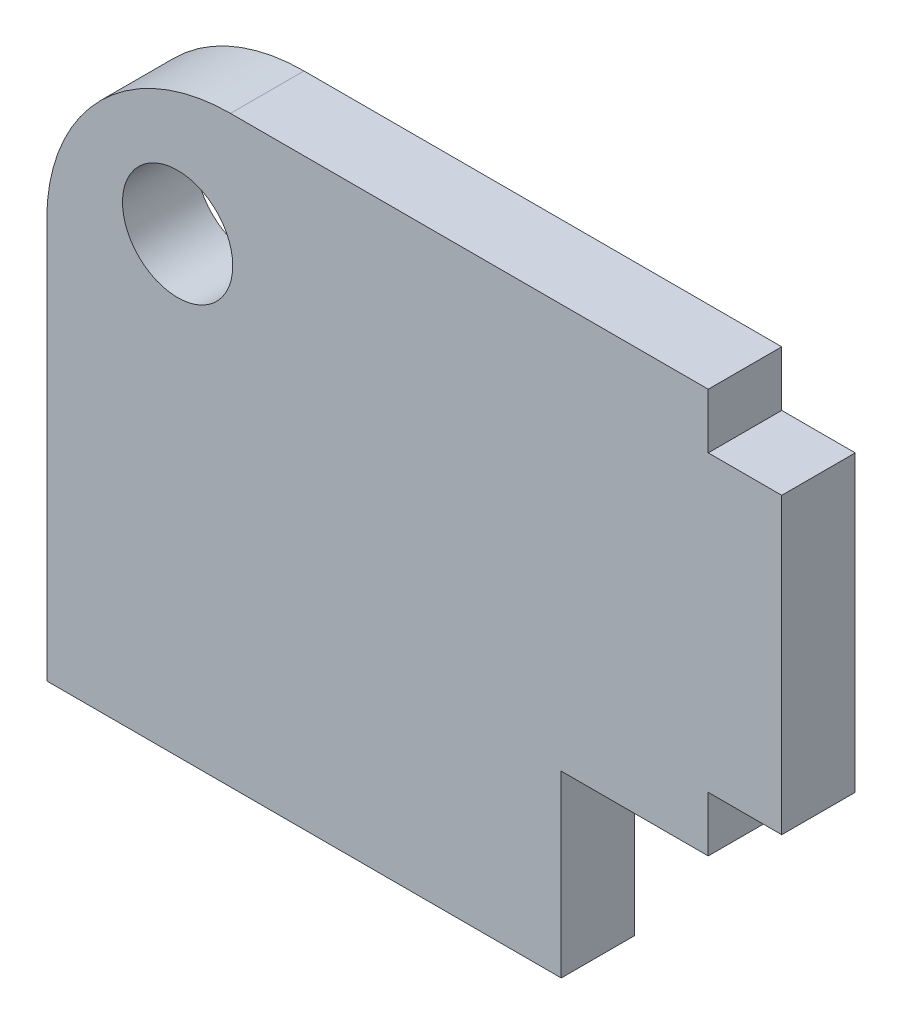
SolidWorks part; units mm, degrees
ref_plane "Front Plane" through (0, 0, 0) normal (0, 0, 1) x (1, 0, 0)
ref_plane "Top Plane" through (0, 0, 0) normal (0, 1, 0) x (1, 0, 0)
ref_plane "Right Plane" through (0, 0, 0) normal (1, 0, 0) x (0, 0, -1)
sketch "Sketch1" plane through (0, 0, 0) normal (0, 0, 1) x (1, 0, 0)
  line L0 (10, -1.5622) -> (8, -1.5622)
  line L1 (4, -7.9378) -> (-10, -7.9378)
  line L2 (4, -7.9378) -> (4, -3.0622)
  line L3 (10, 6.4378) -> (10, -1.5622)
  line L4 (-5, 7.9378) -> (8, 7.9378)
  line L5 (8, 6.4378) -> (8, 7.9378)
  line L6 (10, 6.4378) -> (8, 6.4378)
  line L7 (-10, -7.9378) -> (-10, 2.9378)
  line L8 (8, -1.5622) -> (8, -3.0622)
  line L9 (8, -3.0622) -> (4, -3.0622)
  arc A0 (-10, 2.9378) -> (-5, 7.9378) centre (-5, 2.9378) cw
  circle A2 centre (-6.4393, 4.3772) radius 1.5
  dimension "D6" = 6.4393
  dimension "D1" = 3
  dimension "D2" = 5
  dimension "D3" = 4
  dimension "D4" = 8
  dimension "D5" = 10
  dimension "D7" = 10
  dimension "D8" = 4.3772
  dimension "D9" = 6.4378
  dimension "D10" = 1.5622
  dimension "D13" = 7.9378
extrude "Boss-Extrude1" add sketch "Sketch1" along normal blind 2
